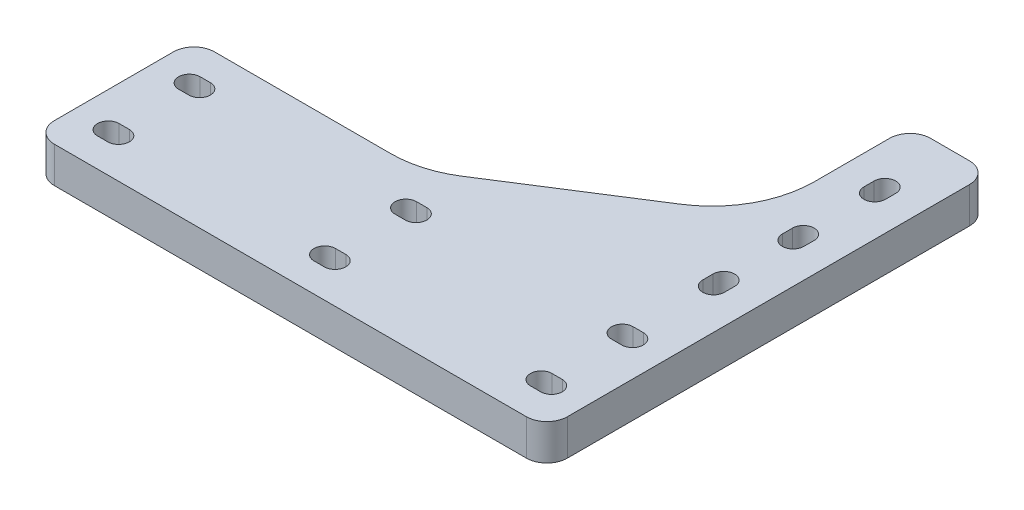
SolidWorks part; units mm, degrees
ref_plane "Front Plane" through (0, 0, 0) normal (0, 0, 1) x (1, 0, 0)
ref_plane "Top Plane" through (0, 0, 0) normal (0, 1, 0) x (1, 0, 0)
ref_plane "Right Plane" through (0, 0, 0) normal (1, 0, 0) x (0, 0, -1)
sketch "Sketch1" plane through (0, 0, 0) normal (0, 1, 0) x (1, 0, 0)
  line L0 (53.594, 73.787) -> (53.594, 71.247) construction
  line L1 (58.42, -19.812) -> (-58.42, -19.812)
  line L2 (63.5, -14.732) -> (63.5, 14.732)
  line L3 (-14.7669, 19.812) -> (-58.42, 19.812)
  line L4 (-63.5, -14.732) -> (-63.5, 14.732)
  line L5 (43.688, 84.836) -> (43.688, 66.2619)
  line L6 (-1.1234, 23.7874) -> (31.9315, 44.8373)
  line L7 (58.42, 89.916) -> (48.768, 89.916)
  line L8 (63.5, 84.836) -> (63.5, 14.732)
  line L9 (56.261, 73.787) -> (56.261, 71.247)
  line L11 (50.927, 73.787) -> (50.927, 71.247)
  line L12 (53.594, 51.054) -> (53.594, 53.594) construction
  line L13 (50.927, 51.054) -> (50.927, 53.594)
  line L14 (56.261, 51.054) -> (56.261, 53.594)
  line L15 (53.594, 31.369) -> (53.594, 33.909) construction
  line L16 (50.927, 31.369) -> (50.927, 33.909)
  line L17 (56.261, 31.369) -> (56.261, 33.909)
  line L19 (-63.5, -10.033) -> (63.5, -10.033) construction
  line L20 (-63.5, 0) -> (63.5, 0) construction
  line L21 (-63.5, 10.033) -> (63.5, 10.033) construction
  line L22 (-54.864, -10.033) -> (-52.324, -10.033) construction
  line L23 (-54.864, -7.366) -> (-52.324, -7.366)
  line L24 (-54.864, -12.7) -> (-52.324, -12.7)
  line L25 (54.864, -10.033) -> (52.324, -10.033) construction
  line L26 (54.864, -12.7) -> (52.324, -12.7)
  line L27 (54.864, -7.366) -> (52.324, -7.366)
  line L28 (-1.27, -10.033) -> (1.27, -10.033) construction
  line L29 (-1.27, -7.366) -> (1.27, -7.366)
  line L30 (-1.27, -12.7) -> (1.27, -12.7)
  line L31 (-54.864, 10.033) -> (-52.324, 10.033) construction
  line L32 (-54.864, 7.366) -> (-52.324, 7.366)
  line L33 (-54.864, 12.7) -> (-52.324, 12.7)
  line L34 (54.864, 10.033) -> (52.324, 10.033) construction
  line L35 (54.864, 12.7) -> (52.324, 12.7)
  line L36 (54.864, 7.366) -> (52.324, 7.366)
  line L37 (-1.27, 10.033) -> (1.27, 10.033) construction
  line L38 (-1.27, 7.366) -> (1.27, 7.366)
  line L39 (-1.27, 12.7) -> (1.27, 12.7)
  circle A0 centre (53.594, 52.324) radius 2.159 construction
  circle A1 centre (53.594, 72.517) radius 2.032 construction
  circle A2 centre (53.594, 32.639) radius 2.032 construction
  arc A3 (56.261, 73.787) -> (50.927, 73.787) centre (53.594, 73.787) ccw
  arc A4 (50.927, 71.247) -> (56.261, 71.247) centre (53.594, 71.247) ccw
  arc A5 (50.927, 51.054) -> (56.261, 51.054) centre (53.594, 51.054) ccw
  arc A6 (56.261, 53.594) -> (50.927, 53.594) centre (53.594, 53.594) ccw
  arc A7 (50.927, 31.369) -> (56.261, 31.369) centre (53.594, 31.369) ccw
  arc A8 (56.261, 33.909) -> (50.927, 33.909) centre (53.594, 33.909) ccw
  arc A9 (-54.864, -7.366) -> (-54.864, -12.7) centre (-54.864, -10.033) ccw
  arc A10 (-52.324, -12.7) -> (-52.324, -7.366) centre (-52.324, -10.033) ccw
  arc A11 (54.864, -12.7) -> (54.864, -7.366) centre (54.864, -10.033) ccw
  arc A12 (52.324, -7.366) -> (52.324, -12.7) centre (52.324, -10.033) ccw
  arc A13 (-1.27, -7.366) -> (-1.27, -12.7) centre (-1.27, -10.033) ccw
  arc A14 (1.27, -12.7) -> (1.27, -7.366) centre (1.27, -10.033) ccw
  arc A15 (-54.864, 7.366) -> (-54.864, 12.7) centre (-54.864, 10.033) cw
  arc A16 (-52.324, 12.7) -> (-52.324, 7.366) centre (-52.324, 10.033) cw
  arc A17 (54.864, 12.7) -> (54.864, 7.366) centre (54.864, 10.033) cw
  arc A18 (52.324, 7.366) -> (52.324, 12.7) centre (52.324, 10.033) cw
  arc A19 (-1.27, 7.366) -> (-1.27, 12.7) centre (-1.27, 10.033) cw
  arc A20 (1.27, 12.7) -> (1.27, 7.366) centre (1.27, 10.033) cw
  arc A21 (48.768, 89.916) -> (43.688, 84.836) centre (48.768, 84.836) ccw
  arc A22 (58.42, 89.916) -> (63.5, 84.836) centre (58.42, 84.836) cw
  arc A23 (58.42, -19.812) -> (63.5, -14.732) centre (58.42, -14.732) ccw
  arc A24 (-58.42, -19.812) -> (-63.5, -14.732) centre (-58.42, -14.732) cw
  arc A25 (-58.42, 19.812) -> (-63.5, 14.732) centre (-58.42, 14.732) ccw
  arc A26 (-14.7669, 19.812) -> (-1.1234, 23.7874) centre (-14.7669, 45.212) ccw
  arc A27 (43.688, 66.2619) -> (31.9315, 44.8373) centre (18.288, 66.2619) cw
  point P0 (0, 0)
  point P9 (0, 0)
  point P17 (53.594, 89.916)
  point P20 (53.594, 72.517)
  point P27 (53.594, 52.324)
  point P34 (53.594, 32.639)
  point P49 (-53.594, -10.033)
  point P55 (53.594, -10.033)
  point P63 (0, -10.033)
  point P70 (-53.594, 10.033)
  point P77 (53.594, 10.033)
  point P84 (0, 10.033)
  point P91 (43.688, 89.916)
  point P94 (63.5, 89.916)
  point P97 (63.5, -19.812)
  point P100 (-63.5, -19.812)
  point P103 (-63.5, 19.812)
  dimension "D5" = 4.064
  dimension "D6" = 4.318
  dimension "D7" = 4.064
  dimension "D8" = 16.002
  dimension "D9" = 15.494
  dimension "D10" = 2.667
  dimension "D14" = 5.08
  dimension "D16" = 25.4
  dimension "D1" = 39.624
  dimension "D2" = 19.812
  dimension "D3" = 109.728
  dimension "D4" = 127
  dimension "D11" = 2.54
  dimension "D12" = 10.033
  dimension "D13" = 9.906
  dimension "D15" = 37.592
extrude "Boss-Extrude2" add sketch "Sketch1" along normal blind 8.89
